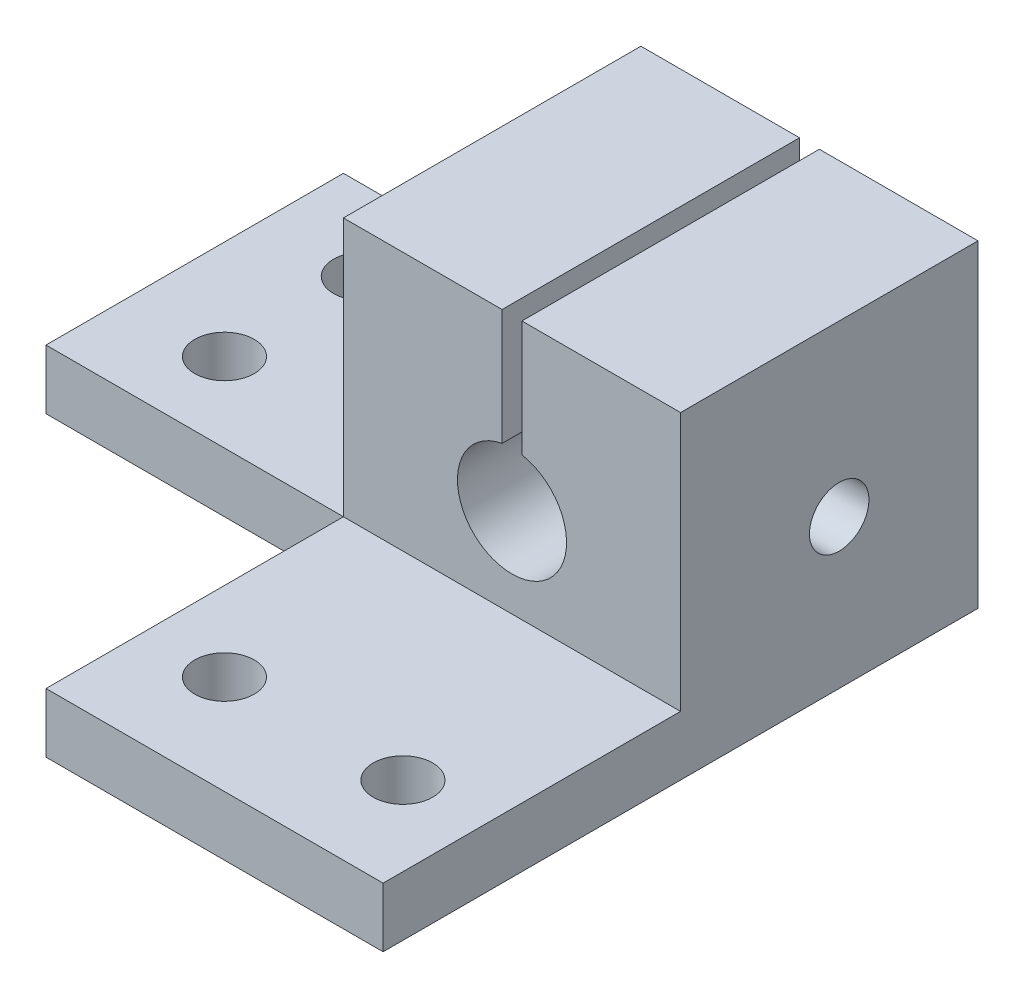
SolidWorks part; units mm, degrees
ref_plane "Front Plane" through (0, 0, 0) normal (0, 0, 1) x (1, 0, 0)
ref_plane "Top Plane" through (0, 0, 0) normal (0, 1, 0) x (1, 0, 0)
ref_plane "Right Plane" through (0, 0, 0) normal (1, 0, 0) x (0, 0, -1)
sketch "Croquis1" plane through (0, 0, 0) normal (0, 1, 0) x (1, 0, 0)
  line L1 (-20, 7.5) -> (20, 7.5)
  line L2 (-20, 7.5) -> (-20, -7.5)
  line L3 (-20, -7.5) -> (20, -7.5)
  line L4 (20, 7.5) -> (20, -7.5)
  line L5 (-20, 7.5) -> (20, -7.5) construction
  line L6 (-20, -7.5) -> (20, 7.5) construction
  line L7 (-8.5, -7.5) -> (8.5, -7.5)
  line L8 (-8.5, -7.5) -> (-8.5, 7.5)
  line L9 (-8.5, 7.5) -> (8.5, 7.5)
  line L10 (8.5, -7.5) -> (8.5, 7.5)
  line L11 (-8.5, -7.5) -> (8.5, 7.5) construction
  line L12 (-8.5, 7.5) -> (8.5, -7.5) construction
  point P0 (0, 0)
  point P7 (0, 0)
  dimension "D1" = 40
  dimension "D2" = 15
  dimension "D3" = 17
  dimension "D4" = 15
extrude "Saliente-Extruir1" add sketch "Croquis1" along normal blind 20 contours L3 L10 L1 L8
sketch "Croquis2" plane through (0, 0, -7.5) normal (0, 0, -1) x (-1, 0, 0)
  line L0 (8.5, 0) -> (-8.5, 0) construction
  line L1 (-0.5, 20) -> (-0.5, 10.2042)
  line L2 (8.5, 20) -> (-8.5, 20) construction
  line L3 (0, 20) -> (0, 31.0218) construction
  line L4 (0.5, 20) -> (0.5, 10.2042)
  circle A0 centre (0, 7.5) radius 2.75
  dimension "D1" = 5.5
  dimension "D2" = 7.5
  dimension "D3" = 0.5
extrude "Cortar-Extruir1" cut sketch "Croquis2" against normal blind 20
sketch "Croquis4" plane through (-8.5, 0, 0) normal (-1, 0, 0) x (0, 0, 1)
  line L0 (-7.5, 20) -> (-7.5, 0) construction
  line L2 (7.5, 0) -> (-7.5, 0) construction
  circle A0 centre (-0.5, 7.5) radius 1.5
  dimension "D1" = 3
  dimension "D2" = 7
  dimension "D3" = 7.5
extrude "Cortar-Extruir3" cut sketch "Croquis4" against normal blind 20
sketch "Croquis7" plane through (0, 0, 7.5) normal (0, 0, 1) x (1, 0, 0)
  line L0 (11.8812, 20) -> (11.8812, 16.0516)
  line L1 (11.8812, 16.0516) -> (-9.4573, 16.0516)
  line L2 (-9.4573, 16.0516) -> (-9.4573, 20)
  line L3 (-9.4573, 20) -> (12.3691, 20)
  line M1 (8.5, 20) -> (0.5, 20)
  line M2 (0.5, 20) -> (0.5, 10.2042)
  line M4 (-0.5, 10.2042) -> (-0.5, 20)
  line M5 (-0.5, 20) -> (-8.5, 20)
  line M6 (-8.5, 20) -> (-8.5, 0)
  line M8 (8.5, 0) -> (8.5, 20)
extrude "Cortar-Extruir5" cut sketch "Croquis7" against normal blind 35 contours L1 M8 M1 M2 | L1 M4 M5 M6
sketch "Croquis8" plane through (0, 0, 7.5) normal (0, 0, 1) x (1, 0, 0)
  line L0 (8.5, 0) -> (8.5, 3)
  line L1 (8.5, 16.0516) -> (8.5, 0) construction
  line L2 (8.5, 3) -> (-8.5, 3)
  line L3 (-8.5, 16.0516) -> (-8.5, 0) construction
  line L4 (-8.5, 3) -> (-8.5, 0)
  line L5 (-8.5, 0) -> (8.5, 0)
  dimension "D1" = 3
extrude "Saliente-Extruir2" add sketch "Croquis8" along normal blind 15
sketch "Croquis9" plane through (-8.5, 0, 0) normal (-1, 0, 0) x (0, 0, 1)
  line L0 (7.5, 3) -> (7.5, 0)
  line L1 (22.5, 0) -> (-7.5, 0) construction
  line L2 (7.5, 0) -> (-7.5, 0)
  line L3 (-7.5, 0) -> (-7.5, 3)
  line L4 (-7.5, 16.0516) -> (-7.5, 0) construction
  line L5 (-7.5, 3) -> (7.5, 3)
extrude "Saliente-Extruir3" add sketch "Croquis9" along normal blind 15
sketch "Croquis10" plane through (0, 0, 0) normal (0, -1, 0) x (1, 0, 0)
  line L0 (-23.5, 7.5) -> (-8.5, 7.5) construction
  line L1 (-23.5, -7.5) -> (8.5, -7.5) construction
  line L2 (-8.5, 22.5) -> (-8.5, 7.5) construction
  line L3 (8.5, 22.5) -> (8.5, -7.5) construction
  line L5 (-8.5, 22.5) -> (8.5, 22.5) construction
  line L6 (-23.5, -7.5) -> (-23.5, 7.5) construction
  circle A1 centre (-18.5, -3.5) radius 1.5
  circle A2 centre (-4.5, 17.5) radius 1.5
  circle A3 centre (4.5, 17.5) radius 1.5
  circle A4 centre (-18.5, 3.5) radius 1.5
  point P19 (0, 0)
  point P22 (-18.5, 3.5)
  point P23 (-23.5, 3.4285)
  dimension "D1" = 3
  dimension "D2" = 3
  dimension "D3" = 5
  dimension "D4" = 3
  dimension "D5" = 4
  dimension "D6" = 4
  dimension "D7" = 4
  dimension "D8" = 4
  dimension "D10" = 5
  dimension "D11" = 3
  dimension "D12" = 5
  dimension "D9" = 5
extrude "Cortar-Extruir6" cut sketch "Croquis10" against normal blind 10
